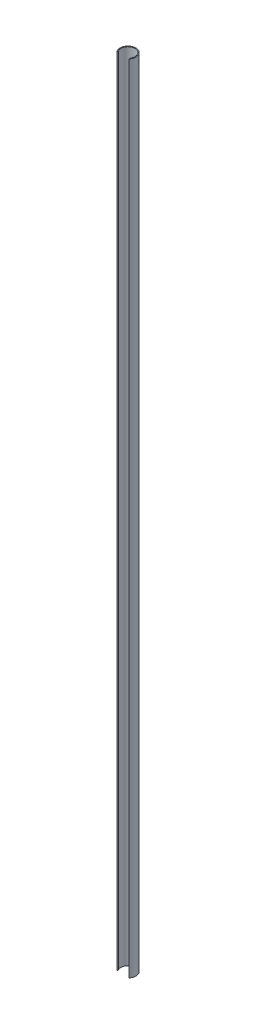
SolidWorks part; units mm, degrees
ref_plane "Front Plane" through (0, 0, 0) normal (0, 0, 1) x (1, 0, 0)
ref_plane "Top Plane" through (0, 0, 0) normal (0, 1, 0) x (1, 0, 0)
ref_plane "Right Plane" through (0, 0, 0) normal (1, 0, 0) x (0, 0, -1)
sketch "Sketch1" plane through (0, 0, 0) normal (0, 1, 0) x (1, 0, 0)
  circle A0 centre (0, 0) radius 0.9017
  circle A1 centre (0, 0) radius 0.8001
  dimension "D1" = 1.8034
  dimension "D2" = 1.6002
extrude "Boss-Extrude1" add sketch "Sketch1" along normal blind 90
sketch "Sketch2" plane through (0, 90, 0) normal (0, 1, 0) x (1, 0, 0)
  line L0 (0, 0) -> (0, -0.9017) construction
  line L1 (0.7, -0.9017) -> (-0.7, -0.9017)
  line L2 (0.7, -0.9017) -> (0.7, -0.2789)
  line L3 (0.7, -0.2789) -> (-0.7, -0.2789)
  line L4 (-0.7, -0.9017) -> (-0.7, -0.2789)
  circle A0 centre (0, 0) radius 0.9017 construction
  point P10 (0, -0.9017)
  dimension "D1" = 1.4
extrude "Cut-Extrude1" cut sketch "Sketch2" against normal blind 90
